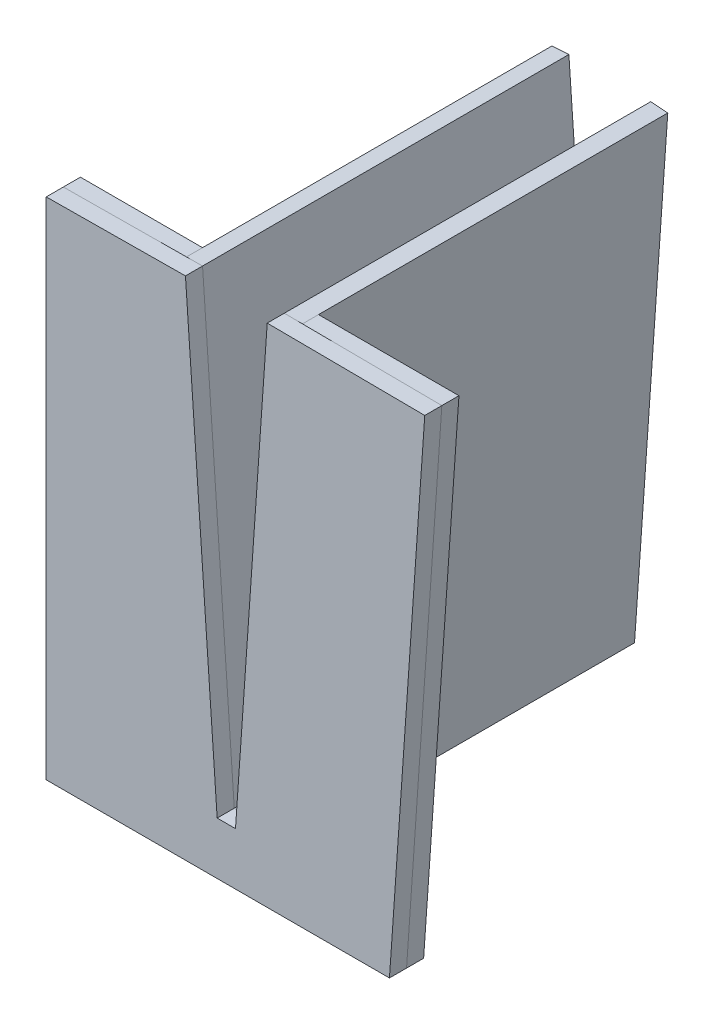
SolidWorks part; units mm, degrees
ref_plane "Front" through (0, 0, 0) normal (0, 0, 1) x (1, 0, 0)
ref_plane "Top" through (0, 0, 0) normal (0, 1, 0) x (1, 0, 0)
ref_plane "Right" through (0, 0, 0) normal (1, 0, 0) x (0, 0, -1)
sketch "Sketch1" plane through (0, 0, 0) normal (0, 0, 1) x (1, 0, 0)
  line L0 (-1.25, 0) -> (-6.6956, 77.8758)
  line L1 (2.5, 17.8758) -> (-2.5, 17.8758) construction
  line L2 (-6.6956, 77.8758) -> (-9.4956, 77.68)
  line L3 (-4.05, -0.1958) -> (-9.4956, 77.68)
  line L4 (1.25, 0) -> (6.6956, 77.8758)
  line L6 (6.6956, 77.8758) -> (9.4956, 77.68)
  line L7 (4.05, -0.1958) -> (9.4956, 77.68)
  line L8 (0, 0) -> (0, 77.8758) construction
  line L9 (0, 77.8758) -> (-6.6956, 77.8758) construction
  line L10 (0, 77.8758) -> (6.6956, 77.8758) construction
  line L11 (-4.05, -0.1958) -> (-1.25, 0)
  line L12 (1.25, 0) -> (4.05, -0.1958)
  line L13 (-1.25, 0) -> (1.25, 0) construction
  point P12 (0, 0)
  point P15 (0, 17.8758)
  dimension "D1" = 5
  dimension "D2" = 8
  dimension "D3" = 2.8
  dimension "D4" = 2.5
  dimension "D5" = 60
extrude "Boss-Extrude1" add sketch "Sketch1" along normal mid plane 60
sketch "Sketch2" plane through (0, 0, 30) normal (0, 0, 1) x (1, 0, 0)
  line L0 (-1.5, 3.5752) -> (1.5, 3.5752)
  line L1 (-9.4956, 77.68) -> (-29.4956, 77.68)
  line L2 (-29.4956, 77.68) -> (-29.4956, -5)
  line L3 (-29.4956, -5) -> (26.7141, -5)
  line L4 (32.4956, 77.68) -> (26.7141, -5)
  line L5 (-1.25, 0) -> (-6.6956, 77.8758) construction
  line L6 (1.25, 0) -> (6.6956, 77.8758) construction
  line L7 (-1.5, 3.5752) -> (-1.25, 0)
  line L8 (-4.05, -0.1958) -> (-9.4956, 77.68) construction
  line L9 (-1.25, 0) -> (-4.05, -0.1958)
  line L10 (-4.05, -0.1958) -> (-9.4956, 77.68)
  line L11 (4.05, -0.1958) -> (9.4956, 77.68) construction
  line L12 (32.4956, 77.68) -> (9.4956, 77.68)
  line L13 (9.4956, 77.68) -> (4.05, -0.1958)
  line L15 (6.6956, 77.8758) -> (9.4956, 77.68) construction
  line L16 (4.05, -0.1958) -> (1.25, 0)
  line L17 (1.25, 0) -> (1.5, 3.5752)
  line L18 (9.4956, 77.68) -> (0.5175, 78.3078) construction
  dimension "D1" = 5
  dimension "D2" = 3
  dimension "D3" = 9
  dimension "D4" = 20
  dimension "D5" = 23
extrude "Boss-Extrude2" add sketch "Sketch2" against normal blind 2.8 separate body
sketch "Sketch3" plane through (0, 0, 30) normal (0, 0, 1) x (1, 0, 0)
  line L5 (-6.6956, 77.8758) -> (-29.4956, 77.68)
  line L6 (-29.4956, 77.68) -> (-29.4956, -5)
  line L7 (-29.4956, -5) -> (26.7141, -5)
  line L8 (26.7141, -5) -> (32.4956, 77.68)
  line L9 (32.4956, 77.68) -> (6.6956, 77.8758)
  line L11 (-1.5, 3.5752) -> (1.5, 3.5752)
  line L12 (-6.6956, 77.8758) -> (-1.5, 3.5752)
  line L15 (1.5, 3.5752) -> (-1.5, 3.5752) construction
  line L16 (6.6956, 77.8758) -> (1.5, 3.5752)
  line L17 (-1.25, 0) -> (-6.6956, 77.8758) construction
extrude "Boss-Extrude3" add sketch "Sketch3" along normal blind 2.8 separate body
